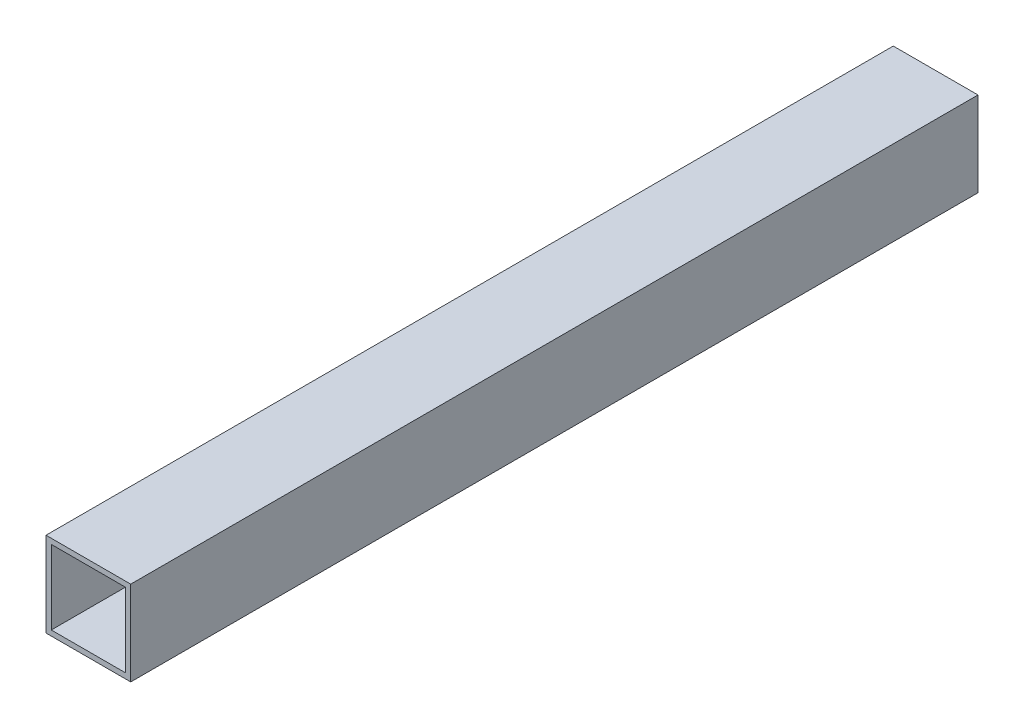
SolidWorks part; units mm, degrees
ref_plane "Front Plane" through (0, 0, 0) normal (0, 0, 1) x (1, 0, 0)
ref_plane "Top Plane" through (0, 0, 0) normal (0, 1, 0) x (1, 0, 0)
ref_plane "Right Plane" through (0, 0, 0) normal (1, 0, 0) x (0, 0, -1)
sketch "Sketch1" plane through (0, 0, 0) normal (0, 0, 1) x (1, 0, 0)
  line L0 (3.175, 47.625) -> (47.625, 47.625)
  line L1 (0, 0) -> (50.8, 0)
  line L2 (0, 0) -> (0, 50.8)
  line L3 (0, 50.8) -> (50.8, 50.8)
  line L4 (50.8, 0) -> (50.8, 50.8)
  line L5 (47.625, 3.175) -> (47.625, 47.625)
  line L6 (3.175, 3.175) -> (47.625, 3.175)
  line L7 (3.175, 3.175) -> (3.175, 47.625)
  dimension "D1" = 50.8
  dimension "D2" = 3.175
extrude "Boss-Extrude1" add sketch "Sketch1" along normal blind 508
